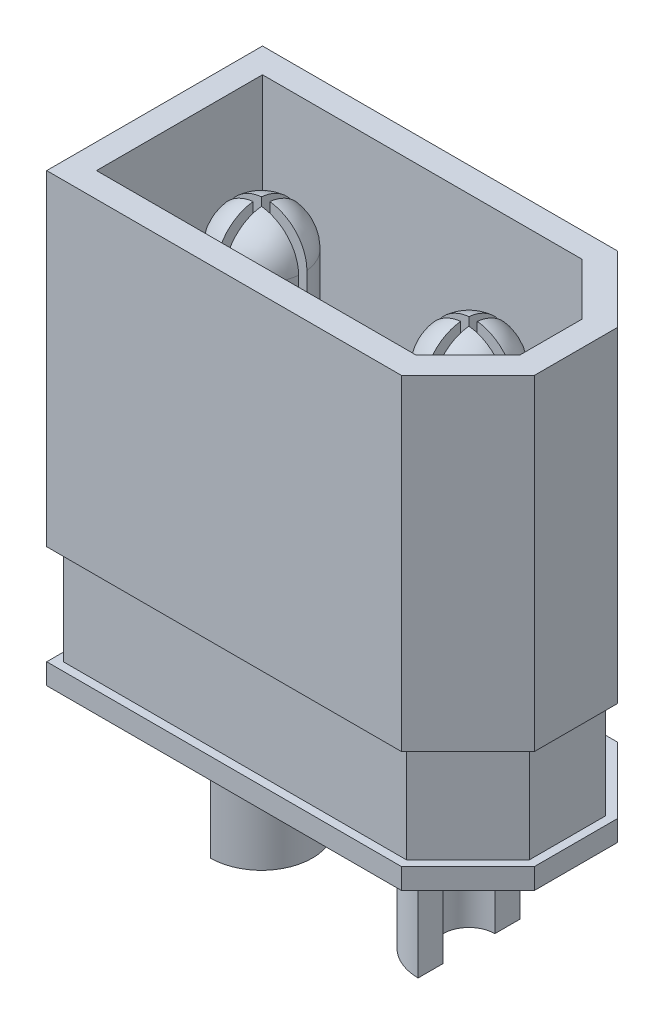
SolidWorks part; units mm, degrees
ref_plane "Front Plane" through (0, 0, 0) normal (0, 0, 1) x (1, 0, 0)
ref_plane "Top Plane" through (0, 0, 0) normal (0, 1, 0) x (1, 0, 0)
ref_plane "Right Plane" through (0, 0, 0) normal (1, 0, 0) x (0, 0, -1)
sketch "Sketch1" plane through (0, 0, 0) normal (0, 1, 0) x (1, 0, 0)
  line L0 (5.075, 1) -> (3.475, 2.6)
  line L1 (-5.075, 2.6) -> (5.075, 2.6)
  line L2 (-5.075, 2.6) -> (-5.075, -2.6)
  line L3 (-5.075, -2.6) -> (5.075, -2.6)
  line L4 (5.075, 2.6) -> (5.075, -2.6)
  line L5 (-5.075, 2.6) -> (5.075, -2.6) construction
  line L6 (-5.075, -2.6) -> (5.075, 2.6) construction
  line L7 (-5.075, 0) -> (5.075, 0) construction
  line L8 (5.075, -1) -> (3.475, -2.6)
  point P0 (0, 0)
  dimension "D1" = 5.2
  dimension "D2" = 10.15
  dimension "D3" = 2
  dimension "D4" = 45
extrude "Shape" add sketch "Sketch1" along normal blind 10.75 contours L8 L4 L0 L1 L2 L3
sketch "Sketch2" plane through (0, 10.75, 0) normal (0, 1, 0) x (1, 0, 0)
  line L12 (3.2265, -2) -> (4.475, -0.7515)
  line L13 (4.475, -0.7515) -> (4.475, 0.7515)
  line L14 (4.475, 0.7515) -> (3.2265, 2)
  line L15 (3.2265, 2) -> (-4.475, 2)
  line L16 (-4.475, 2) -> (-4.475, -2)
  line L17 (-4.475, -2) -> (3.2265, -2)
  line L18 (3.2265, -2) -> (4.475, -0.7515)
  line L19 (4.475, -0.7515) -> (4.475, 0.7515)
  line L20 (4.475, 0.7515) -> (3.2265, 2)
  line L21 (3.2265, 2) -> (-4.475, 2)
  line L22 (-4.475, 2) -> (-4.475, -2)
  line L23 (-4.475, -2) -> (3.2265, -2)
  dimension "D1" = 0.6
extrude "Cut-Extrude1" cut sketch "Sketch2" against normal blind 6.75
sketch "Sketch3" plane through (0, 4, 0) normal (0, 1, 0) x (1, 0, 0)
  line L0 (-4.475, 0) -> (4.475, 0) construction
  line L1 (-4.475, 2) -> (-4.475, -2) construction
  line L2 (4.475, -0.7515) -> (4.475, 0.7515) construction
  line L3 (0, 2) -> (0, -2) construction
  line L4 (3.2265, 2) -> (-4.475, 2) construction
  line L5 (-4.475, -2) -> (3.2265, -2) construction
  line L7 (1.6754, -1.6) -> (-1.6754, -1.6)
  line L8 (1.6754, -1.6) -> (1.6754, 1.6)
  line L9 (1.6754, 1.6) -> (-1.6754, 1.6)
  line L10 (-1.6754, -1.6) -> (-1.6754, 1.6)
  line L11 (1.6754, -1.6) -> (-1.6754, 1.6) construction
  line L12 (1.6754, 1.6) -> (-1.6754, -1.6) construction
  circle A0 centre (-2.5, 0) radius 1.8
  circle A1 centre (2.5, 0) radius 1.8
  point P15 (0, 0)
  dimension "D2" = 3.6
  dimension "D1" = 5
  dimension "D3" = 3.2
extrude "Cut-Extrude2" cut sketch "Sketch3" against normal up to next contours L7 A1 L9 A0
fillet "Fillet1" radius 0.2 4 edges at (-1.6754, 2, 1.6) (1.6754, 2, 1.6) (1.6754, 2, -1.6) (-1.6754, 2, -1.6)
sketch "Sketch4" plane through (0, 4, 0) normal (0, 1, 0) x (1, 0, 0)
  line L0 (0, 2) -> (0, -2) construction
  line L13 (-4.475, 2) -> (3.2265, 2) construction
  line L14 (-4.475, -2) -> (3.2265, -2) construction
  circle A0 centre (-2.5, 0) radius 1
  circle A2 centre (2.5, 0) radius 1
  dimension "D1" = 2
extrude "Boss-Extrude2" add sketch "Sketch4" along normal offset from surface (6.1 mm away) 0.65 up to face at (1.0755, 10.75, 0)
fillet "Fillet2" radius 1 2 edges at (2.5, 10.1, 1) (-2.5, 10.1, 1)
sketch "Sketch5" plane through (0, 10.75, 0) normal (0, 1, 0) x (1, 0, 0)
  line L0 (0, 2.6) -> (0, -2.6) construction
  line L1 (-2.6, 1) -> (-2.4, 1)
  line L2 (-2.6, 1) -> (-2.6, -1)
  line L3 (-2.6, -1) -> (-2.4, -1)
  line L4 (-2.4, 1) -> (-2.4, -1)
  line L5 (-2.6, 1) -> (-2.4, -1) construction
  line L6 (-2.6, -1) -> (-2.4, 1) construction
  line L7 (-1.5, 0.1) -> (-3.5, 0.1)
  line L8 (-1.5, 0.1) -> (-1.5, -0.1)
  line L9 (-1.5, -0.1) -> (-3.5, -0.1)
  line L10 (-3.5, 0.1) -> (-3.5, -0.1)
  line L11 (-1.5, 0.1) -> (-3.5, -0.1) construction
  line L12 (-1.5, -0.1) -> (-3.5, 0.1) construction
  line L13 (-5.075, 2.6) -> (3.475, 2.6) construction
  line L14 (-5.075, -2.6) -> (3.475, -2.6) construction
  line L15 (1.5, 0.1) -> (1.5, -0.1)
  line L16 (1.5, -0.1) -> (3.5, -0.1)
  line L17 (3.5, 0.1) -> (3.5, -0.1)
  line L18 (1.5, 0.1) -> (3.5, 0.1)
  line L19 (2.6, 1) -> (2.4, 1)
  line L20 (2.4, 1) -> (2.4, -1)
  line L21 (2.6, -1) -> (2.4, -1)
  line L22 (2.6, 1) -> (2.6, -1)
  circle A0 centre (-2.5, 0) radius 1 construction
  point P0 (-2.5, 0)
  point P8 (-2.5, 0)
  dimension "D1" = 0.2
extrude "Cut-Extrude3" cut sketch "Sketch5" against normal up to surface (6.75 mm away) contours L4 L3 L2 L1 | L7 L10 L9 L8 | L16 L17 L18 L15 | L20 L21 L22 L19 up to face at (2.5, 4, 1)
ref_plane "Plane1" through (0, 0.5, 0) normal (0, -1, 0) x (-1, 0, 0)
sketch "Sketch6" plane through (0, 0.5, 0) normal (0, -1, 0) x (-1, 0, 0)
  line L13 (-4.875, -0.9172) -> (-3.3922, -2.4)
  line L14 (-3.3922, -2.4) -> (4.875, -2.4)
  line L15 (4.875, -2.4) -> (4.875, 2.4)
  line L16 (4.875, 2.4) -> (-3.3922, 2.4)
  line L17 (-3.3922, 2.4) -> (-4.875, 0.9172)
  line L18 (-4.875, 0.9172) -> (-4.875, -0.9172)
  line L19 (-4.875, -0.9172) -> (-3.3922, -2.4)
  line L20 (-3.3922, -2.4) -> (4.875, -2.4)
  line L21 (4.875, -2.4) -> (4.875, 2.4)
  line L22 (4.875, 2.4) -> (-3.3922, 2.4)
  line L23 (-3.3922, 2.4) -> (-4.875, 0.9172)
  line L24 (-4.875, 0.9172) -> (-4.875, -0.9172)
  line L25 (-5.075, -1) -> (-3.475, -2.6)
  line L26 (-3.475, -2.6) -> (5.075, -2.6)
  line L27 (5.075, -2.6) -> (5.075, 2.6)
  line L28 (5.075, 2.6) -> (-3.475, 2.6)
  line L29 (-3.475, 2.6) -> (-5.075, 1)
  line L30 (-5.075, 1) -> (-5.075, -1)
  line L31 (-5.075, -1) -> (-3.475, -2.6)
  line L32 (-3.475, -2.6) -> (5.075, -2.6)
  line L33 (5.075, -2.6) -> (5.075, 2.6)
  line L34 (5.075, 2.6) -> (-3.475, 2.6)
  line L35 (-3.475, 2.6) -> (-5.075, 1)
  line L36 (-5.075, 1) -> (-5.075, -1)
  dimension "D1" = 0.2
  dimension "D2" = 0
extrude "Cut-Extrude4" cut sketch "Sketch6" against normal blind 2.4
sketch "Sketch8" plane through (0, 0, 0) normal (0, -1, 0) x (1, 0, 0)
  line L7 (-4.475, -2) -> (-4.475, 2) construction
  line L8 (3.2265, -2) -> (-4.475, -2) construction
  line L9 (4.475, -0.7515) -> (3.2265, -2) construction
  line L10 (4.475, 0.7515) -> (4.475, -0.7515) construction
  line L11 (3.2265, 2) -> (4.475, 0.7515) construction
  line L12 (-4.475, 2) -> (3.2265, 2) construction
  line L13 (-4.475, -2) -> (-4.475, 2)
  line L14 (3.2265, -2) -> (-4.475, -2)
  line L15 (4.475, -0.7515) -> (3.2265, -2)
  line L16 (4.475, 0.7515) -> (4.475, -0.7515)
  line L17 (3.2265, 2) -> (4.475, 0.7515)
  line L24 (-4.475, 2) -> (3.2265, 2)
extrude "Cut-Extrude5" cut sketch "Sketch8" against normal blind 1
sketch "Sketch7" plane through (0, 1, 0) normal (0, -1, 0) x (1, 0, 0)
  line L0 (0, 1.6) -> (0, -1.6) construction
  line L1 (-1.0717, 1.6) -> (1.0717, 1.6) construction
  line L2 (-1.0717, -1.6) -> (1.0717, -1.6) construction
  circle A0 centre (-2.5, 0) radius 1.225
  arc A1 (-2.4, -0.995) -> (-1.505, -0.1) centre (-2.5, 0) ccw construction
  circle A2 centre (-2.5, 0) radius 0.625
  circle A3 centre (2.5, 0) radius 0.625
  circle A4 centre (2.5, 0) radius 1.225
  dimension "D1" = 0.6
  dimension "D2" = 2.45
extrude "Boss-Extrude3" add sketch "Sketch7" along normal blind 4
sketch "Sketch9" plane through (0, -3, 0) normal (0, -1, 0) x (1, 0, 0)
  line L0 (0, 1.6) -> (0, -1.6) construction
  line L1 (-2.5, 1.225) -> (-3.725, 1.225)
  line L2 (-2.5, 1.225) -> (-2.5, -1.225)
  line L3 (-2.5, -1.225) -> (-3.725, -1.225)
  line L4 (-3.725, 1.225) -> (-3.725, -1.225)
  line L5 (-1.0717, 1.6) -> (1.0717, 1.6) construction
  line L6 (-1.0717, -1.6) -> (1.0717, -1.6) construction
  line L7 (-2.5, 1.225) -> (-2.5, -1.225) construction
  line L8 (2.5, 1.225) -> (3.725, 1.225)
  line L9 (2.5, 1.225) -> (2.5, -1.225)
  line L10 (2.5, -1.225) -> (3.725, -1.225)
  line L11 (3.725, 1.225) -> (3.725, -1.225)
  circle A0 centre (-2.5, 0) radius 1.225 construction
  circle A1 centre (-2.5, 0) radius 1.225 construction
extrude "Cut-Extrude6" cut sketch "Sketch9" against normal blind 2.3
